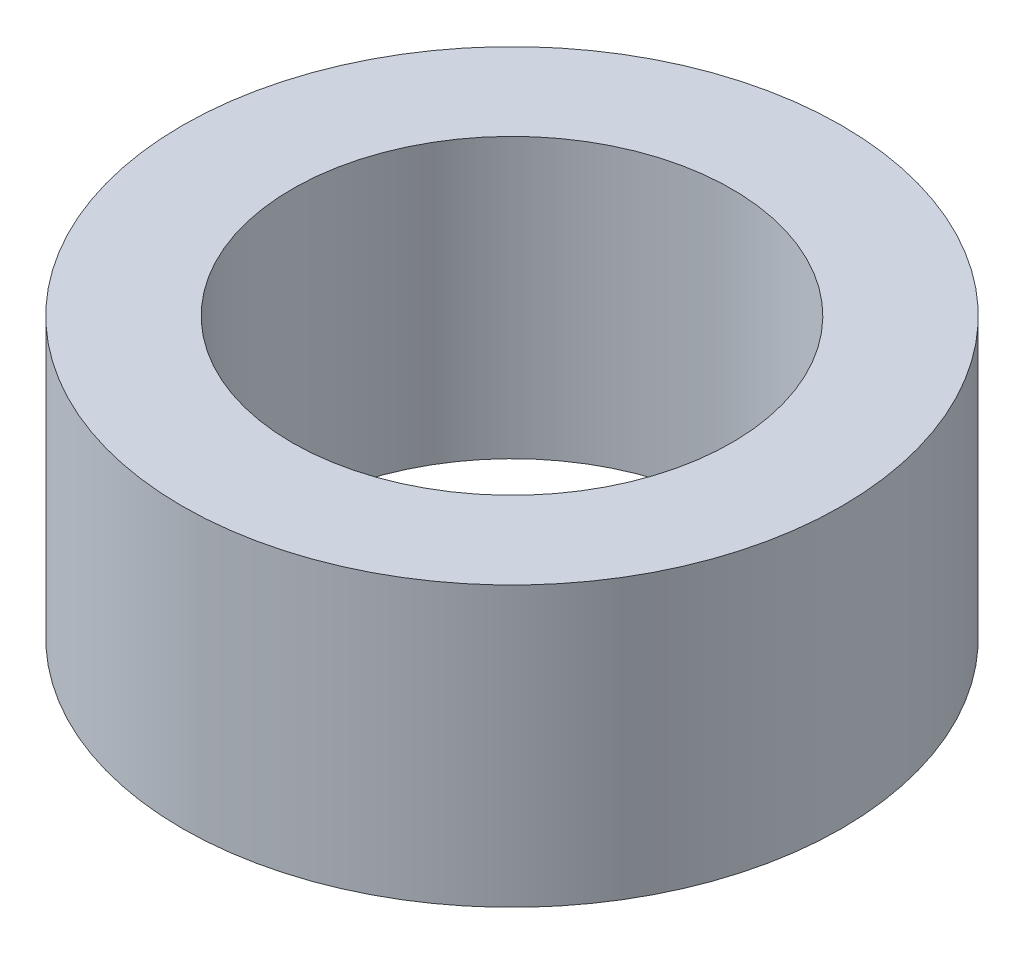
SolidWorks part; units mm, degrees
ref_plane "Front Plane" through (0, 0, 0) normal (0, 0, 1) x (1, 0, 0)
ref_plane "Top Plane" through (0, 0, 0) normal (0, 1, 0) x (1, 0, 0)
ref_plane "Right Plane" through (0, 0, 0) normal (1, 0, 0) x (0, 0, -1)
sketch "Sketch1" plane through (0, 0, 0) normal (0, 1, 0) x (1, 0, 0)
  circle A0 centre (0, 0) radius 5
  circle A1 centre (0, 0) radius 7.5
  dimension "D1" = 15
  dimension "D2" = 10
extrude "Boss-Extrude1" add sketch "Sketch1" along normal blind 6.35
